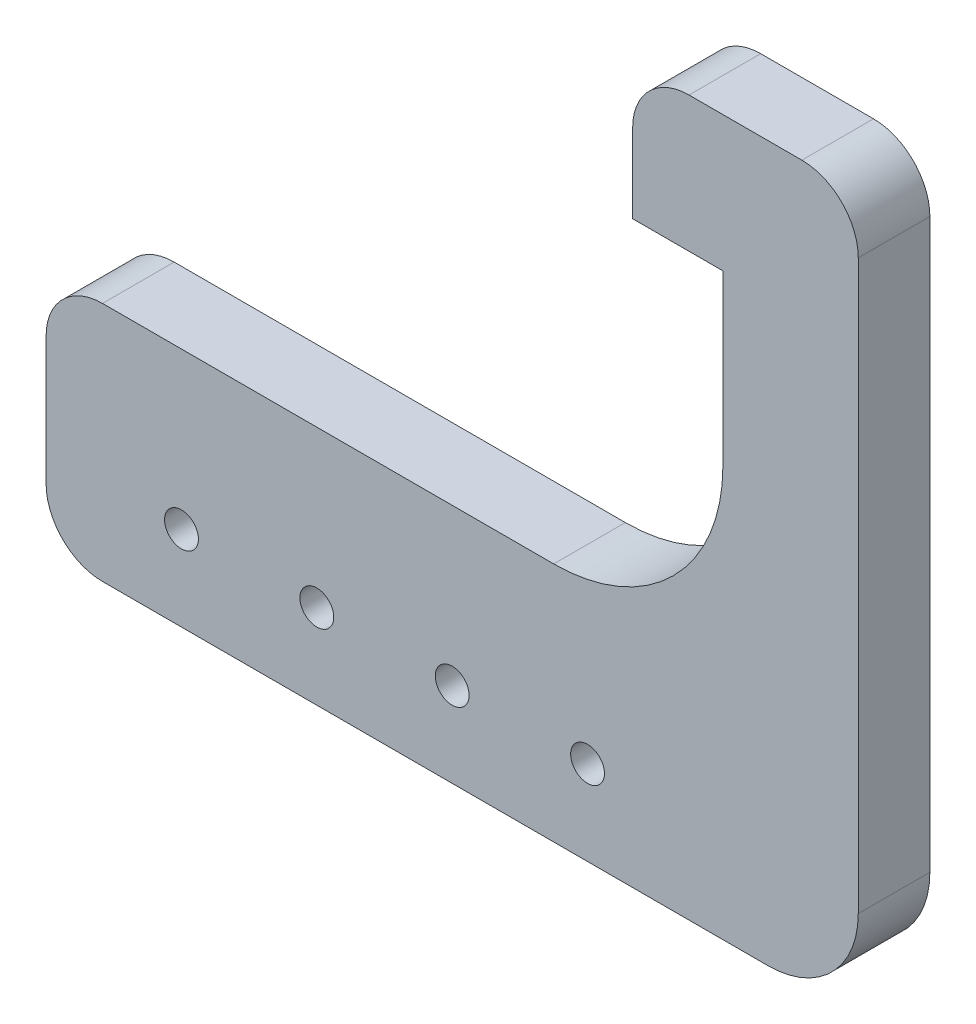
SolidWorks part; units mm, degrees
ref_plane "Front Plane" through (0, 0, 0) normal (0, 0, 1) x (1, 0, 0)
ref_plane "Top Plane" through (0, 0, 0) normal (0, 1, 0) x (1, 0, 0)
ref_plane "Right Plane" through (0, 0, 0) normal (1, 0, 0) x (0, 0, -1)
sketch "Sketch1" plane through (0, 0, 0) normal (0, 0, 1) x (1, 0, 0)
  line L1 (0, 0) -> (60, 0)
  line L2 (0, 0) -> (0, 21.35)
  line L3 (0, 21.35) -> (60, 21.35)
  line L4 (60, 0) -> (60, 21.35)
  line L5 (60, 0) -> (72, 0)
  line L6 (60, 0) -> (60, 51.35)
  line L7 (60, 51.35) -> (72, 51.35)
  line L8 (72, 0) -> (72, 51.35)
  line L9 (72, 51.35) -> (52, 51.35)
  line L10 (72, 51.35) -> (72, 63.35)
  line L11 (72, 63.35) -> (52, 63.35)
  line L12 (52, 51.35) -> (52, 63.35)
  circle A0 centre (48, 7.5) radius 1.5
  circle A1 centre (36, 7.5) radius 1.5
  circle A2 centre (24, 7.5) radius 1.5
  circle A3 centre (12, 7.5) radius 1.5
  point P14 (66, 51.35)
  dimension "D7" = 3
  dimension "D1" = 21.35
  dimension "D2" = 60
  dimension "D3" = 30
  dimension "D4" = 12
  dimension "D5" = 12
  dimension "D6" = 20
  dimension "D8" = 12
  dimension "D10" = 7.5
  dimension "D9" = 4
extrude "Boss-Extrude1" add sketch "Sketch1" along normal blind 6.35 contours L1 L4 L3 L2 A3 A2 A1 A0 | L5 L8 L7 L6 L4 | L12 L9 L7 L10 L11
fillet "Fillet1" radius 15 1 edges at (60, 21.35, 3.175)
fillet "Fillet3" radius 5 1 edges at (52, 63.35, 3.175)
fillet "Fillet5" radius 5 2 edges at (0, 21.35, 3.175) (0, 0, 3.175)
fillet "Fillet6" radius 5 1 edges at (72, 63.35, 3.175)
fillet "Fillet7" radius 8 1 edges at (72, 0, 3.175)
